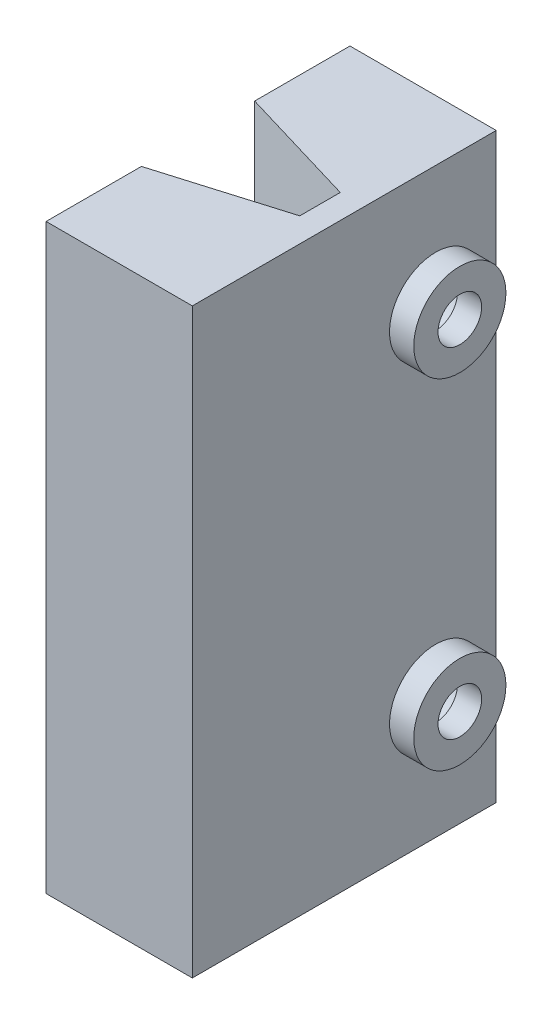
SolidWorks part; units mm, degrees
ref_plane "Front Plane" through (0, 0, 0) normal (0, 0, 1) x (1, 0, 0)
ref_plane "Top Plane" through (0, 0, 0) normal (0, 1, 0) x (1, 0, 0)
ref_plane "Right Plane" through (0, 0, 0) normal (1, 0, 0) x (0, 0, -1)
sketch "Sketch1" plane through (0, 0, 0) normal (0, 1, 0) x (1, 0, 0)
  line L0 (0.7588, 5.315) -> (5, 5.315)
  line L1 (-1.03, 5.315) -> (0.7588, 5.315)
  line L2 (-1.03, 5.315) -> (-1.03, -0.115)
  line L3 (-1.03, -7.215) -> (1.3982, -7.215)
  line L15 (-1.03, -0.115) -> (4, -0.115)
  line L17 (-1.03, -1.785) -> (4, -1.785)
  line L18 (4, -0.115) -> (4, -1.785)
  line L21 (5, 5.315) -> (5, -7.215)
  line L22 (5, -7.215) -> (1.3982, -7.215)
  line L23 (-1.03, -1.785) -> (-1.03, -7.215)
  point P0 (0, 0)
  dimension "D12" = 1
extrude "Boss-Extrude1" add sketch "Sketch1" along normal blind 24
ref_plane "Plane2" through (0, 0, 0.95) normal (0, 0, 1) x (1, 0, 0)
sketch "Sketch3" plane through (5, 0, 0) normal (1, 0, 0) x (0, 0, -1)
  line L0 (5.315, 24) -> (5.315, 0) construction
  line L2 (-7.215, 0) -> (5.315, 0) construction
  line L3 (-7.215, 24) -> (5.315, 24) construction
  circle A0 centre (2.815, 19) radius 0.9
  circle A1 centre (2.815, 5) radius 0.9
  circle A2 centre (2.815, 19) radius 1.9
  circle A3 centre (2.815, 5) radius 1.9
  dimension "D1" = 1.8
  dimension "D2" = 1.8
  dimension "D5" = 5
  dimension "D6" = 5
  dimension "D7" = 1
  dimension "D8" = 1
  dimension "D3" = 2.5
  dimension "D4" = 2.5
extrude "Boss-Extrude2" add sketch "Sketch3" along normal blind 1
sketch "Sketch4" plane through (5, 0, 0) normal (1, 0, 0) x (0, 0, -1)
  circle A0 centre (2.815, 19) radius 1.15
  circle A1 centre (2.815, 5) radius 1.15
extrude "Cut-Extrude2" cut sketch "Sketch4" against normal blind 4
sketch "Sketch6" plane through (0, 24, 0) normal (0, 1, 0) x (1, 0, 0)
  line L0 (4, -0.115) -> (-1.03, 1.385)
  line L1 (-1.03, 5.315) -> (-1.03, -0.115) construction
  line L2 (-1.03, 1.385) -> (-1.03, -0.115)
  line L3 (-1.03, -0.115) -> (4, -0.115)
  line L4 (-1.03, -1.785) -> (4, -1.785)
  line L5 (4, -1.785) -> (-1.03, -3.285)
  line L6 (-1.03, -1.785) -> (-1.03, -7.215) construction
  line M4 (-1.03, 5.315) -> (-1.03, -0.115)
  line M5 (-1.03, -0.115) -> (4, -0.115)
  line M7 (4, -1.785) -> (-1.03, -1.785)
  line M8 (-1.03, -1.785) -> (-1.03, -7.215)
  dimension "D1" = 1.5
  dimension "D2" = 1.5
extrude "Cut-Extrude3" cut sketch "Sketch6" against normal blind 30 contours L0 M5 M4 | L5 M7 M8
